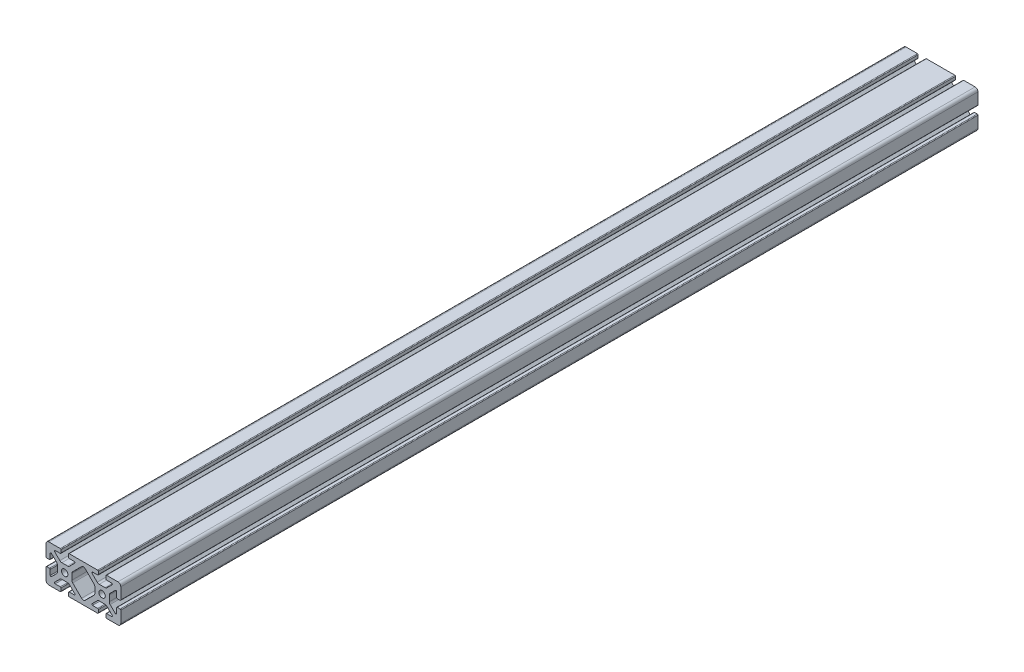
SolidWorks part; units mm, degrees
ref_plane "Front Plane" through (0, 0, 0) normal (0, 0, 1) x (1, 0, 0)
ref_plane "Top Plane" through (0, 0, 0) normal (0, 1, 0) x (1, 0, 0)
ref_plane "Right Plane" through (0, 0, 0) normal (1, 0, 0) x (0, 0, -1)
sketch "Sketch1" plane through (0, 0, 0) normal (0, 0, 1) x (1, 0, 0)
  line L2 (-39.878, 16.891) -> (-39.878, 4.7625)
  line L3 (-36.83, 19.939) -> (-24.7015, 19.939)
  line L4 (-23.9395, 19.177) -> (-23.9395, 16.2052)
  line L5 (-24.7015, 15.4432) -> (-30.1625, 15.4432)
  line L6 (-30.7013, 14.1424) -> (-25.133, 8.5741)
  line L7 (-34.0814, 10.7623) -> (-28.5131, 5.194)
  line L8 (-35.3822, 10.2235) -> (-35.3822, 4.7625)
  line L9 (-36.1442, 4.0005) -> (-39.116, 4.0005)
  line L11 (-23.0136, 7.6962) -> (-16.8644, 7.6962)
  line L12 (-27.6352, 3.0746) -> (-27.6352, -3.0746)
  line L13 (15.1765, 19.939) -> (-15.1765, 19.939)
  line L14 (-15.9385, 19.177) -> (-15.9385, 16.2052)
  line L15 (-15.1765, 15.4432) -> (-9.7155, 15.4432)
  line L16 (-12.2428, 3.0746) -> (-12.2428, -3.0746)
  line L17 (-9.1767, 14.1424) -> (-14.745, 8.5741)
  line L18 (-1.9047, 14.6543) -> (-11.3649, 5.194)
  line L19 (-36.1442, -4.0005) -> (-39.116, -4.0005)
  line L20 (-35.3822, -10.2235) -> (-35.3822, -4.7625)
  line L21 (-34.0814, -10.7623) -> (-28.5131, -5.194)
  line L22 (-30.7013, -14.1424) -> (-25.133, -8.5741)
  line L23 (-24.7015, -15.4432) -> (-30.1625, -15.4432)
  line L24 (-23.9395, -19.177) -> (-23.9395, -16.2052)
  line L25 (-36.83, -19.939) -> (-24.7015, -19.939)
  line L26 (-39.878, -16.891) -> (-39.878, -4.7625)
  line L27 (15.1765, -19.939) -> (-15.1765, -19.939)
  line L28 (-15.9385, -19.177) -> (-15.9385, -16.2052)
  line L29 (-15.1765, -15.4432) -> (-9.7155, -15.4432)
  line L30 (-9.1767, -14.1424) -> (-14.745, -8.5741)
  line L31 (-1.9047, -14.6543) -> (-11.3649, -5.194)
  line L32 (-23.0136, -7.6962) -> (-16.8644, -7.6962)
  line L34 (23.0136, -7.6962) -> (16.8644, -7.6962)
  line L35 (1.9047, -14.6543) -> (11.3649, -5.194)
  line L36 (9.1767, -14.1424) -> (14.745, -8.5741)
  line L37 (15.1765, -15.4432) -> (9.7155, -15.4432)
  line L38 (15.9385, -19.177) -> (15.9385, -16.2052)
  line L40 (39.878, -16.891) -> (39.878, -4.7625)
  line L41 (36.83, -19.939) -> (24.7015, -19.939)
  line L42 (23.9395, -19.177) -> (23.9395, -16.2052)
  line L43 (24.7015, -15.4432) -> (30.1625, -15.4432)
  line L44 (30.7013, -14.1424) -> (25.133, -8.5741)
  line L45 (34.0814, -10.7623) -> (28.5131, -5.194)
  line L46 (35.3822, -10.2235) -> (35.3822, -4.7625)
  line L47 (36.1442, -4.0005) -> (39.116, -4.0005)
  line L48 (1.9047, 14.6543) -> (11.3649, 5.194)
  line L49 (9.1767, 14.1424) -> (14.745, 8.5741)
  line L50 (12.2428, 3.0746) -> (12.2428, -3.0746)
  line L51 (15.1765, 15.4432) -> (9.7155, 15.4432)
  line L52 (15.9385, 19.177) -> (15.9385, 16.2052)
  line L53 (27.6352, 3.0746) -> (27.6352, -3.0746)
  line L54 (23.0136, 7.6962) -> (16.8644, 7.6962)
  line L55 (36.1442, 4.0005) -> (39.116, 4.0005)
  line L56 (35.3822, 10.2235) -> (35.3822, 4.7625)
  line L57 (34.0814, 10.7623) -> (28.5131, 5.194)
  line L58 (30.7013, 14.1424) -> (25.133, 8.5741)
  line L59 (24.7015, 15.4432) -> (30.1625, 15.4432)
  line L60 (23.9395, 19.177) -> (23.9395, 16.2052)
  line L61 (36.83, 19.939) -> (24.7015, 19.939)
  line L62 (39.878, 16.891) -> (39.878, 4.7625)
  circle A0 centre (-19.939, 0) radius 3.4036
  arc A1 (-39.878, 16.891) -> (-36.83, 19.939) centre (-36.83, 16.891) cw
  arc A2 (-34.0814, 10.7623) -> (-35.3822, 10.2235) centre (-34.6202, 10.2235) ccw
  arc A3 (-30.1625, 15.4432) -> (-30.7013, 14.1424) centre (-30.1625, 14.6812) ccw
  arc A4 (-24.7015, 19.939) -> (-23.9395, 19.177) centre (-24.7015, 19.177) cw
  arc A5 (-39.878, 4.7625) -> (-39.116, 4.0005) centre (-39.116, 4.7625) ccw
  arc A6 (-35.3822, 4.7625) -> (-36.1442, 4.0005) centre (-36.1442, 4.7625) cw
  arc A7 (-23.9395, 16.2052) -> (-24.7015, 15.4432) centre (-24.7015, 16.2052) cw
  arc A8 (-23.0136, 7.6962) -> (-25.133, 8.5741) centre (-23.0136, 10.6934) cw
  arc A9 (-27.6352, 3.0746) -> (-28.5131, 5.194) centre (-30.6324, 3.0746) ccw
  arc A10 (1.9047, 14.6543) -> (-1.9047, 14.6543) centre (0, 12.7496) ccw
  arc A11 (-1.9047, -14.6543) -> (1.9047, -14.6543) centre (0, -12.7496) ccw
  arc A12 (-15.1765, 19.939) -> (-15.9385, 19.177) centre (-15.1765, 19.177) ccw
  arc A13 (-15.9385, 16.2052) -> (-15.1765, 15.4432) centre (-15.1765, 16.2052) ccw
  arc A14 (-16.8644, 7.6962) -> (-14.745, 8.5741) centre (-16.8644, 10.6934) ccw
  arc A15 (-12.2428, 3.0746) -> (-11.3649, 5.194) centre (-9.2456, 3.0746) cw
  arc A16 (-9.7155, 15.4432) -> (-9.1767, 14.1424) centre (-9.7155, 14.6812) cw
  arc A17 (-27.6352, -3.0746) -> (-28.5131, -5.194) centre (-30.6324, -3.0746) cw
  arc A18 (-23.0136, -7.6962) -> (-25.133, -8.5741) centre (-23.0136, -10.6934) ccw
  arc A19 (-23.9395, -16.2052) -> (-24.7015, -15.4432) centre (-24.7015, -16.2052) ccw
  arc A20 (-35.3822, -4.7625) -> (-36.1442, -4.0005) centre (-36.1442, -4.7625) ccw
  arc A21 (-39.878, -4.7625) -> (-39.116, -4.0005) centre (-39.116, -4.7625) cw
  arc A22 (-24.7015, -19.939) -> (-23.9395, -19.177) centre (-24.7015, -19.177) ccw
  arc A23 (-30.1625, -15.4432) -> (-30.7013, -14.1424) centre (-30.1625, -14.6812) cw
  arc A24 (-34.0814, -10.7623) -> (-35.3822, -10.2235) centre (-34.6202, -10.2235) cw
  arc A25 (-39.878, -16.891) -> (-36.83, -19.939) centre (-36.83, -16.891) ccw
  arc A26 (-9.7155, -15.4432) -> (-9.1767, -14.1424) centre (-9.7155, -14.6812) ccw
  arc A27 (-15.1765, -19.939) -> (-15.9385, -19.177) centre (-15.1765, -19.177) cw
  arc A28 (-15.9385, -16.2052) -> (-15.1765, -15.4432) centre (-15.1765, -16.2052) cw
  arc A29 (-16.8644, -7.6962) -> (-14.745, -8.5741) centre (-16.8644, -10.6934) cw
  arc A30 (-12.2428, -3.0746) -> (-11.3649, -5.194) centre (-9.2456, -3.0746) ccw
  arc A31 (12.2428, -3.0746) -> (11.3649, -5.194) centre (9.2456, -3.0746) cw
  arc A32 (16.8644, -7.6962) -> (14.745, -8.5741) centre (16.8644, -10.6934) ccw
  arc A33 (15.9385, -16.2052) -> (15.1765, -15.4432) centre (15.1765, -16.2052) ccw
  arc A34 (15.1765, -19.939) -> (15.9385, -19.177) centre (15.1765, -19.177) ccw
  arc A35 (9.7155, -15.4432) -> (9.1767, -14.1424) centre (9.7155, -14.6812) cw
  arc A36 (39.878, -16.891) -> (36.83, -19.939) centre (36.83, -16.891) cw
  arc A37 (34.0814, -10.7623) -> (35.3822, -10.2235) centre (34.6202, -10.2235) ccw
  arc A38 (30.1625, -15.4432) -> (30.7013, -14.1424) centre (30.1625, -14.6812) ccw
  arc A39 (24.7015, -19.939) -> (23.9395, -19.177) centre (24.7015, -19.177) cw
  arc A40 (39.878, -4.7625) -> (39.116, -4.0005) centre (39.116, -4.7625) ccw
  arc A41 (35.3822, -4.7625) -> (36.1442, -4.0005) centre (36.1442, -4.7625) cw
  arc A42 (23.9395, -16.2052) -> (24.7015, -15.4432) centre (24.7015, -16.2052) cw
  arc A43 (23.0136, -7.6962) -> (25.133, -8.5741) centre (23.0136, -10.6934) cw
  arc A44 (27.6352, -3.0746) -> (28.5131, -5.194) centre (30.6324, -3.0746) ccw
  arc A45 (9.7155, 15.4432) -> (9.1767, 14.1424) centre (9.7155, 14.6812) ccw
  arc A46 (12.2428, 3.0746) -> (11.3649, 5.194) centre (9.2456, 3.0746) ccw
  arc A47 (16.8644, 7.6962) -> (14.745, 8.5741) centre (16.8644, 10.6934) cw
  arc A48 (15.9385, 16.2052) -> (15.1765, 15.4432) centre (15.1765, 16.2052) cw
  arc A49 (15.1765, 19.939) -> (15.9385, 19.177) centre (15.1765, 19.177) cw
  arc A50 (27.6352, 3.0746) -> (28.5131, 5.194) centre (30.6324, 3.0746) cw
  arc A51 (23.0136, 7.6962) -> (25.133, 8.5741) centre (23.0136, 10.6934) ccw
  arc A52 (23.9395, 16.2052) -> (24.7015, 15.4432) centre (24.7015, 16.2052) ccw
  arc A53 (35.3822, 4.7625) -> (36.1442, 4.0005) centre (36.1442, 4.7625) ccw
  arc A54 (39.878, 4.7625) -> (39.116, 4.0005) centre (39.116, 4.7625) cw
  arc A55 (24.7015, 19.939) -> (23.9395, 19.177) centre (24.7015, 19.177) ccw
  arc A56 (30.1625, 15.4432) -> (30.7013, 14.1424) centre (30.1625, 14.6812) cw
  arc A57 (34.0814, 10.7623) -> (35.3822, 10.2235) centre (34.6202, 10.2235) cw
  arc A58 (39.878, 16.891) -> (36.83, 19.939) centre (36.83, 16.891) ccw
  circle A59 centre (19.939, 0) radius 3.4036
  point P185 (19.939, 7.6962)
extrude "Boss-Extrude1" add sketch "Sketch1" along normal mid plane 914.4
